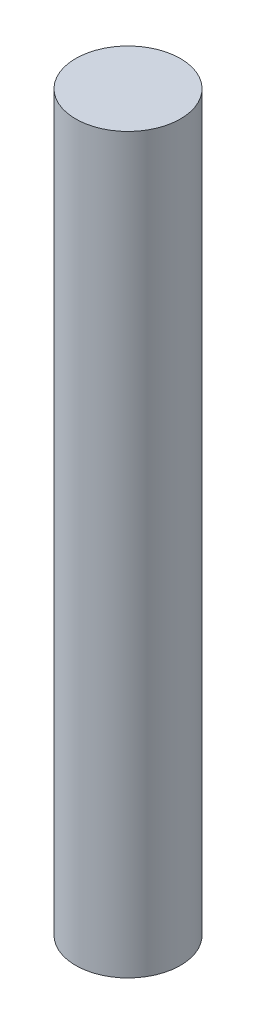
SolidWorks part; units mm, degrees
material "Plain Carbon Steel"
ref_plane "Front Plane" through (0, 0, 0) normal (0, 0, 1) x (1, 0, 0)
ref_plane "Top Plane" through (0, 0, 0) normal (0, 1, 0) x (1, 0, 0)
ref_plane "Right Plane" through (0, 0, 0) normal (1, 0, 0) x (0, 0, -1)
sketch "Sketch1" plane through (0, 0, 0) normal (0, 0, 1) x (1, 0, 0)
  line L0 (0, 0) -> (0, 33.6602) construction
  line L2 (0, 0) -> (1.5, 0)
  line L3 (0, 0) -> (0, 21)
  line L4 (0, 21) -> (1.5, 21)
  line L5 (1.5, 0) -> (1.5, 21)
  dimension "D1" = 21
  dimension "D2" = 3
revolve "Revolve1" add sketch "Sketch1" angle 360 about L0
